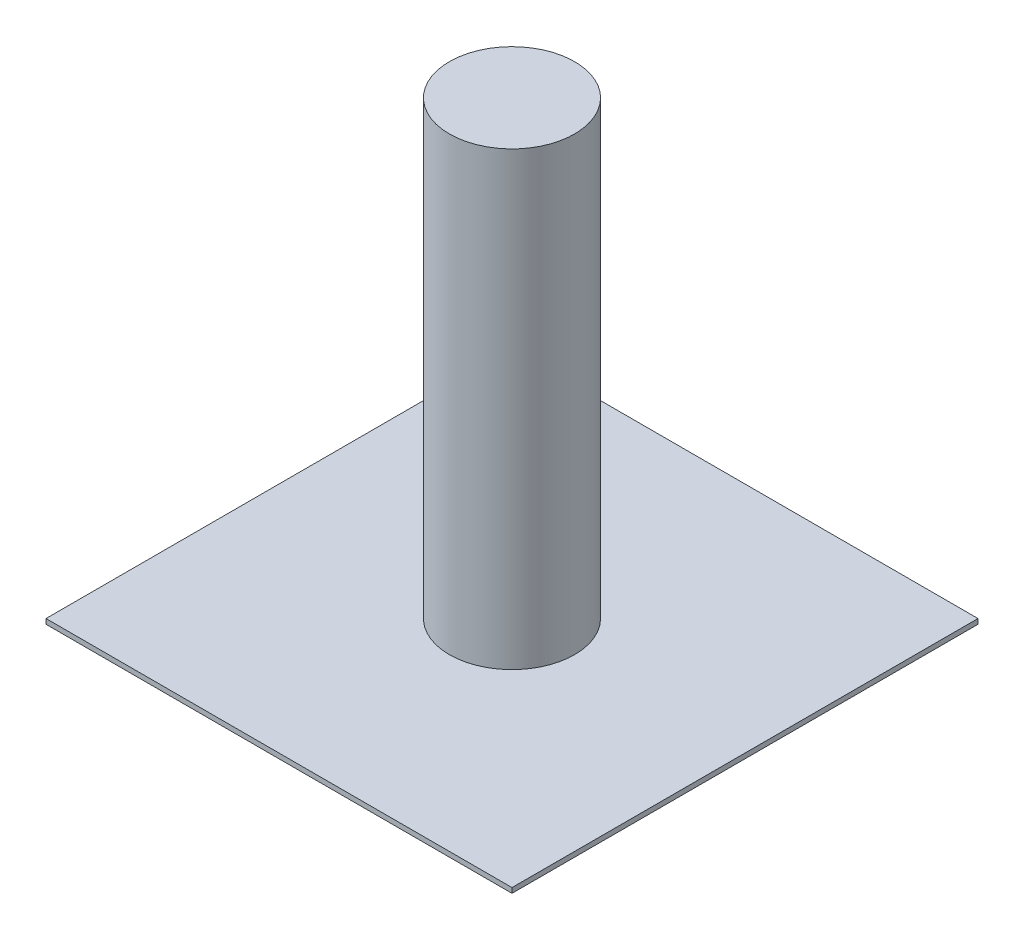
SolidWorks part; units mm, degrees
ref_plane "Front Plane" through (0, 0, 0) normal (0, 0, 1) x (1, 0, 0)
ref_plane "Top Plane" through (0, 0, 0) normal (0, 1, 0) x (1, 0, 0)
ref_plane "Right Plane" through (0, 0, 0) normal (1, 0, 0) x (0, 0, -1)
sketch "Sketch1" plane through (0, 0, 0) normal (0, 1, 0) x (1, 0, 0)
  line L1 (-93, 93) -> (93, 93)
  line L2 (-93, 93) -> (-93, -93)
  line L3 (-93, -93) -> (93, -93)
  line L4 (93, 93) -> (93, -93)
  line L5 (-93, 93) -> (93, -93) construction
  line L6 (-93, -93) -> (93, 93) construction
  point P0 (0, 0)
  dimension "D1" = 186
  dimension "D2" = 186
extrude "Boss-Extrude1" add sketch "Sketch1" along normal blind 2
sketch "Sketch2" plane through (0, 2, 0) normal (0, 1, 0) x (1, 0, 0)
  circle A0 centre (0, 0) radius 25
  dimension "D1" = 50
extrude "Boss-Extrude2" add sketch "Sketch2" along normal blind 180
